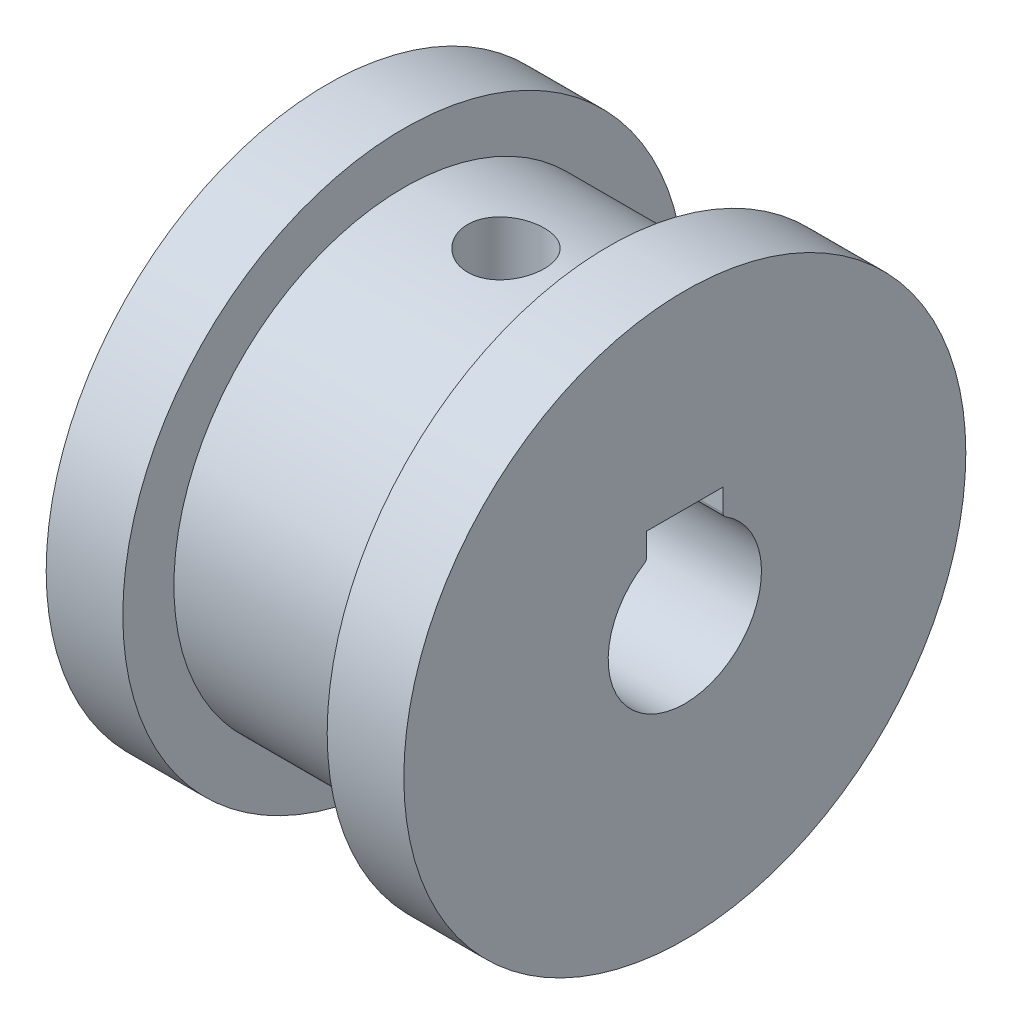
SolidWorks part; units mm, degrees
ref_plane "Piano frontale" through (0, 0, 0) normal (0, 0, 1) x (1, 0, 0)
ref_plane "Piano superiore" through (0, 0, 0) normal (0, 1, 0) x (1, 0, 0)
ref_plane "Piano destro" through (0, 0, 0) normal (1, 0, 0) x (0, 0, -1)
sketch "Sketch1" plane through (0, 0, 0) normal (1, 0, 0) x (0, 0, -1)
  circle A0 centre (0, 0) radius 9
  dimension "D1" = 18
extrude "Boss-Extrude1" add sketch "Sketch1" along normal blind 8
sketch "Sketch2" plane through (8, 0, 0) normal (1, 0, 0) x (0, 0, -1)
  line L0 (0, 4.7697) -> (0, 9) construction
  line L1 (0, 3.5981) -> (0, 4.7697) construction
  line L2 (-1.5, 3.5981) -> (1.5, 3.5981)
  line L3 (-1.5, 3.5981) -> (-1.5, 2.7111)
  line L5 (1.5, 3.5981) -> (1.5, 2.7111)
  arc A0 (-1.5938, 2.5416) -> (1.5938, 2.5416) centre (0, 0) ccw
  circle A1 centre (0, 0) radius 9 construction
  arc A2 (-1.5938, 2.5416) -> (-1.5, 2.7111) centre (-1.7, 2.7111) ccw
  arc A3 (1.5938, 2.5416) -> (1.5, 2.7111) centre (1.7, 2.7111) cw
  point P14 (-1.5, 2.5981)
  dimension "D1" = 6
  dimension "D4" = 0.2
  dimension "D5" = 0.2
  dimension "D2" = 3
  dimension "D3" = 1
sketch "Sketch3" plane through (8, 0, 0) normal (1, 0, 0) x (0, 0, -1)
  circle A0 centre (0, 0) radius 11
  dimension "D1" = 22
extrude "Boss-Extrude2" add sketch "Sketch3" along normal blind 3
sketch "Sketch4" plane through (0, 0, 0) normal (-1, 0, 0) x (0, 0, 1)
  circle A0 centre (0, 0) radius 11
  dimension "D1" = 22
extrude "Boss-Extrude3" add sketch "Sketch4" along normal blind 3
extrude "Cut-Extrude2" cut sketch "Sketch2" against normal blind 11 and the other way blind 3
sketch "Sketch6" plane through (0, 3.5981, 0) normal (0, -1, 0) x (1, 0, 0)
  line L0 (-3, 0) -> (11, 0) construction
  line L1 (-3, -1.5) -> (-3, 1.5) construction
  line L2 (11, -1.5) -> (11, 1.5) construction
  circle A0 centre (4, 0) radius 1.5
  dimension "D1" = 3
extrude "Cut-Extrude3" cut sketch "Sketch6" against normal blind 6
